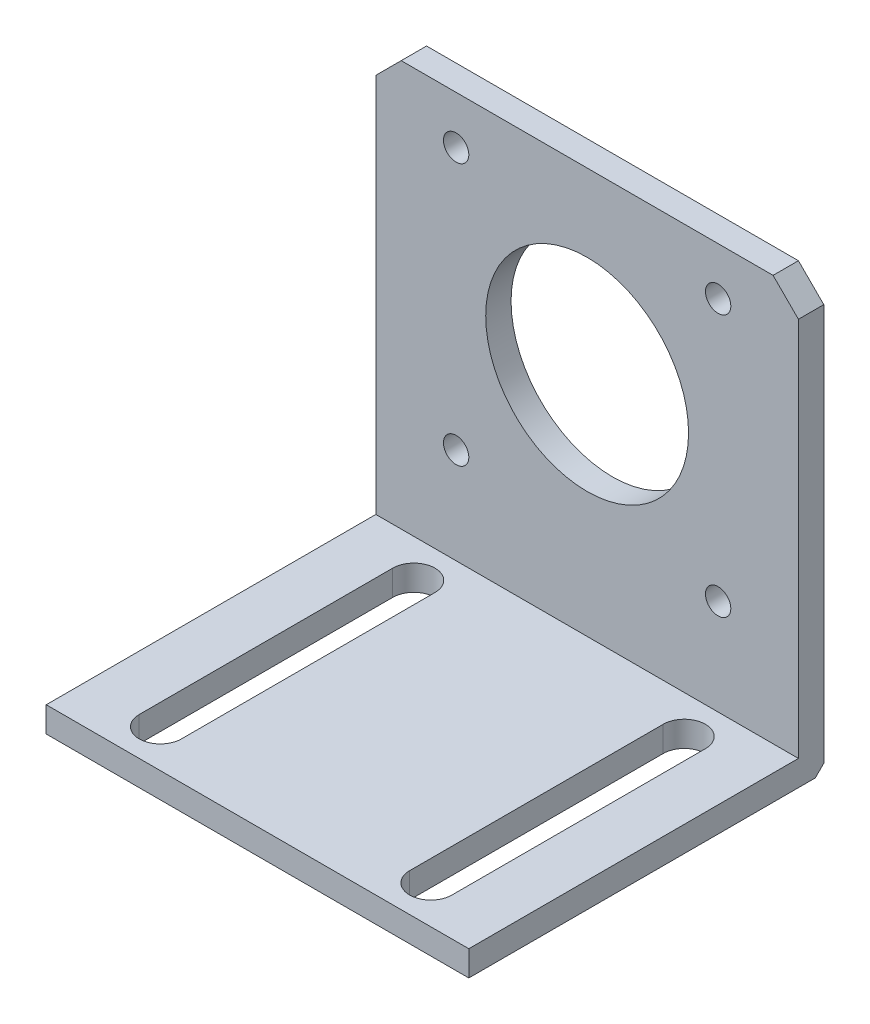
SolidWorks part; units mm, degrees
ref_plane "Front Plane" through (0, 0, 0) normal (0, 0, 1) x (1, 0, 0)
ref_plane "Top Plane" through (0, 0, 0) normal (0, 1, 0) x (1, 0, 0)
ref_plane "Right Plane" through (0, 0, 0) normal (1, 0, 0) x (0, 0, -1)
sketch "Sketch1" plane through (0, 0, 0) normal (0, 0, 1) x (1, 0, 0)
  line L5 (-22, 21.15) -> (-25, 18.15)
  line L6 (22, 21.15) -> (-22, 21.15)
  line L10 (0, 14.3733) -> (0, -4.5768) construction
  line L11 (0, -55) -> (0, 55) construction
  line L12 (10.3516, 0) -> (-13.5361, 0) construction
  line L13 (25, 18.15) -> (25, -23.85)
  line L14 (21.15, 21.15) -> (-21.15, 21.15) construction
  line L15 (21.15, 21.15) -> (21.15, -21.15) construction
  line L16 (21.15, -21.15) -> (-21.15, -21.15) construction
  line L17 (-21.15, 21.15) -> (-21.15, -21.15) construction
  line L18 (21.15, 21.15) -> (-21.15, -21.15) construction
  line L19 (21.15, -21.15) -> (-21.15, 21.15) construction
  line L20 (22, -26.85) -> (-22, -26.85)
  line L21 (-25, 18.15) -> (-25, -23.85)
  line L22 (25, 21.15) -> (-25, -26.85) construction
  line L23 (25, -26.85) -> (-25, 21.15) construction
  line L24 (25, 18.15) -> (22, 21.15)
  line L25 (25, -23.85) -> (22, -26.85)
  line L26 (-22, -26.85) -> (-25, -23.85)
  circle A4 centre (0, 0) radius 12
  circle A5 centre (-15.5, 15.5) radius 1.5
  circle A6 centre (15.5, 15.5) radius 1.5
  circle A7 centre (-15.5, -15.5) radius 1.5
  circle A8 centre (15.5, -15.5) radius 1.5
  point P1 (0, -2.85)
  point P7 (0, 0)
  point P25 (0, 0)
  dimension "D4" = 50
  dimension "D10" = 24
  dimension "D3" = 3
  dimension "D2" = 48
  dimension "D9" = 15.5
  dimension "D11" = 15.5
  dimension "D12" = 42.3
extrude "Boss-Extrude1" add sketch "Sketch1" along normal blind 3
sketch "Sketch2" plane through (0, 0, 0) normal (0, 0, -1) x (-1, 0, 0)
  line L0 (-25, -23.85) -> (-25, -29.85)
  line L1 (-25, -29.85) -> (25, -29.85)
  line L7 (25, -29.85) -> (25, -23.85)
  line L10 (25, -23.85) -> (22, -26.85)
  line L11 (22, -26.85) -> (-22, -26.85)
  line L12 (-22, -26.85) -> (-25, -23.85)
  dimension "D1" = 3
extrude "Boss-Extrude2" add sketch "Sketch2" against normal blind 3
sketch "Sketch3" plane through (0, 0, 3) normal (0, 0, 1) x (1, 0, 0)
  line L5 (-25, -29.85) -> (-25, -26.85)
  line L6 (-25, 18.15) -> (-25, -29.85) construction
  line L7 (-25, -26.85) -> (25, -26.85)
  line L8 (25, -29.85) -> (25, 18.15) construction
  line L9 (25, -26.85) -> (25, -29.85)
  line L10 (25, -29.85) -> (-25, -29.85)
  dimension "D1" = 3
extrude "Boss-Extrude3" add sketch "Sketch3" along normal blind 39
chamfer "Chamfer1" distance 1 angle 45 1 edges at (0, -29.85, 0)
sketch "Sketch4" plane through (0, -26.85, 0) normal (0, 1, 0) x (1, 0, 0)
  line L0 (16, -7.5) -> (16, -37.5) construction
  line L1 (18.5, -7.5) -> (18.5, -37.5)
  line L2 (13.5, -7.5) -> (13.5, -37.5)
  line L3 (0, -3) -> (0, -42) construction
  line L6 (-16, -7.5) -> (-16, -37.5) construction
  line L7 (-18.5, -7.5) -> (-18.5, -37.5)
  line L8 (-13.5, -7.5) -> (-13.5, -37.5)
  line L9 (25, -42) -> (-25, -42) construction
  arc A0 (18.5, -7.5) -> (13.5, -7.5) centre (16, -7.5) ccw
  arc A1 (13.5, -37.5) -> (18.5, -37.5) centre (16, -37.5) ccw
  arc A2 (-18.5, -7.5) -> (-13.5, -7.5) centre (-16, -7.5) cw
  arc A3 (-13.5, -37.5) -> (-18.5, -37.5) centre (-16, -37.5) cw
  point P2 (16, -22.5)
  point P16 (-16, -22.5)
  dimension "D1" = 2.5
  dimension "D2" = 16
  dimension "D3" = 30
  dimension "D4" = 19.5
extrude "Cut-Extrude1" cut sketch "Sketch4" against normal blind 3
